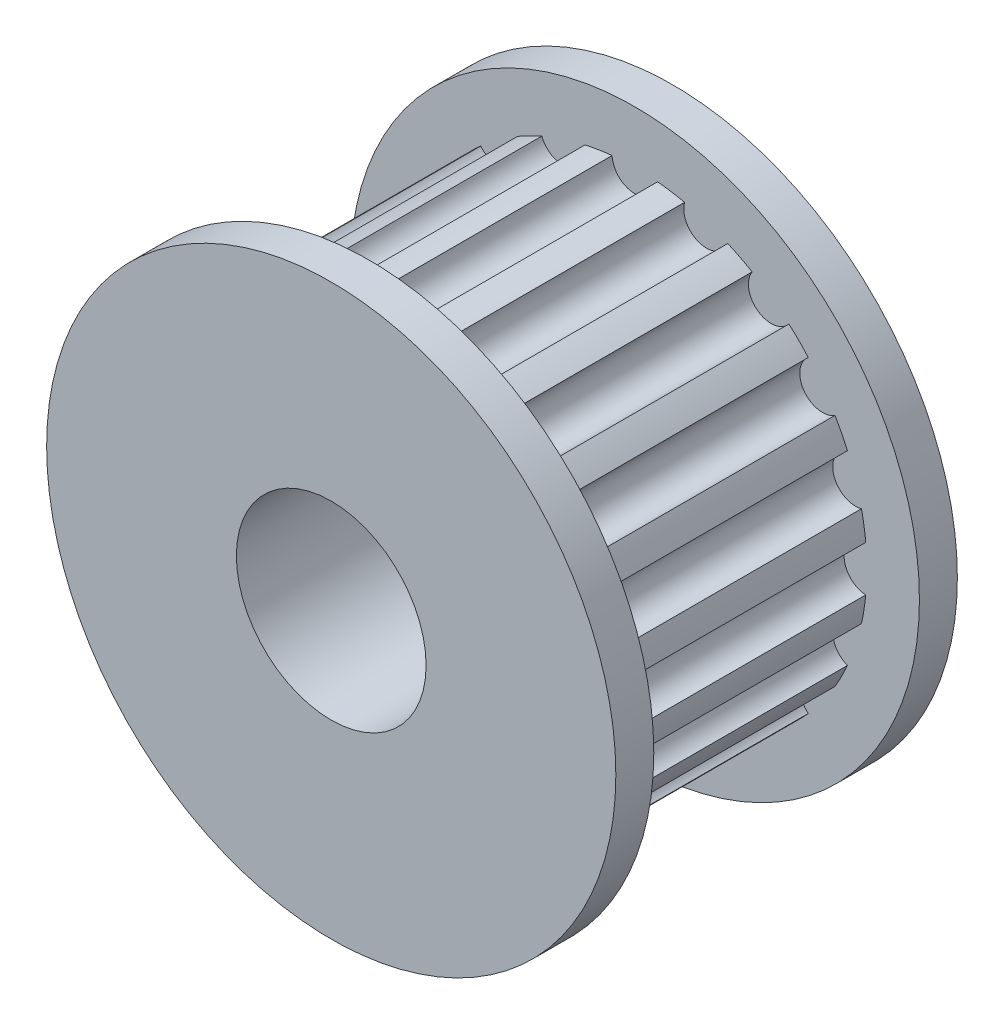
SolidWorks part; units mm, degrees
material "6061 合金"
ref_plane "前基準面" through (0, 0, 0) normal (0, 0, 1) x (1, 0, 0)
ref_plane "上基準面" through (0, 0, 0) normal (0, 1, 0) x (1, 0, 0)
ref_plane "右基準面" through (0, 0, 0) normal (1, 0, 0) x (0, 0, -1)
sketch "草圖1" plane through (0, 0, 0) normal (0, 0, 1) x (1, 0, 0)
  circle A0 centre (0, 0) radius 7.5
  dimension "D1" = 15
extrude "填料-伸長1" add sketch "草圖1" along normal mid plane 1
sketch "草圖2" plane through (0, 0, 0.5) normal (0, 0, 1) x (1, 0, 0)
  circle A0 centre (0, 0) radius 6.115
  dimension "D1" = 12.23
extrude "填料-伸長2" add sketch "草圖2" along normal blind 7
sketch "草圖7" plane through (0, 0, 7.5) normal (0, 0, 1) x (1, 0, 0)
  line L0 (0, 0) -> (0, 6.115) construction
  arc A0 (-0.5993, 6.0856) -> (0.5993, 6.0856) centre (0, 6.115) ccw
  circle A1 centre (0, 0) radius 6.115 construction
  circle A2 centre (0, 0) radius 6.115 construction
  arc A3 (-0.5993, 6.0856) -> (0.5993, 6.0856) centre (0, 0) cw
  point P10 (0, 5.515)
  dimension "D1" = 0.6
extrude "除料-伸長3" cut sketch "草圖7" against normal up to surface (7 mm away) up to face at (6.115, 0, 0.5)
sketch "草圖3" plane through (0, 0, 7.5) normal (0, 0, 1) x (1, 0, 0)
  circle A0 centre (0, 0) radius 7.5
  circle A1 centre (0, 0) radius 7.5 construction
extrude "填料-伸長3" add sketch "草圖3" along normal blind 1
sketch "草圖6" plane through (0, 0, -0.5) normal (0, 0, -1) x (-1, 0, 0)
  circle A0 centre (0, 0) radius 2.5
  dimension "D1" = 5
extrude "除料-伸長2" cut sketch "草圖6" against normal through all
pattern_circular "環狀複製排列2" count 20 over 360 about axis through (0, 0, 0) along (0, 0, 1) of "除料-伸長3"
